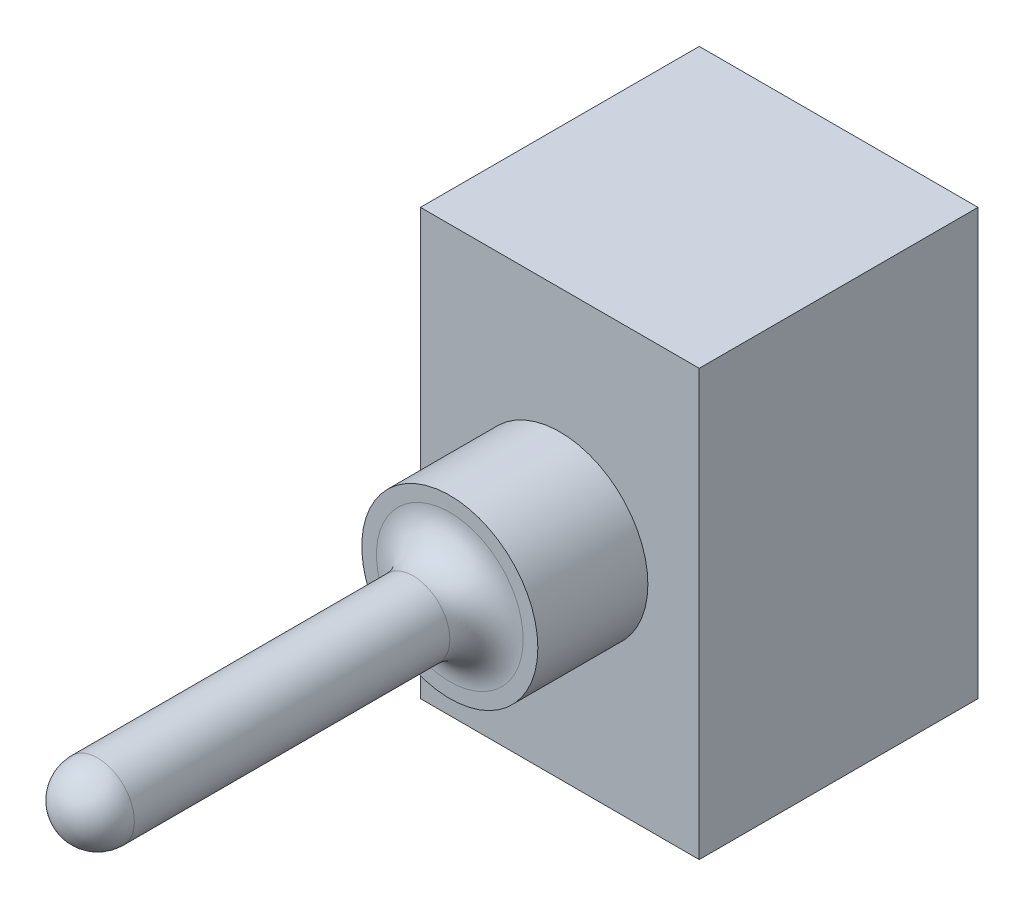
SolidWorks part; units mm, degrees
ref_plane "Plan de face" through (0, 0, 0) normal (0, 0, 1) x (1, 0, 0)
ref_plane "Plan de dessus" through (0, 0, 0) normal (0, 1, 0) x (1, 0, 0)
ref_plane "Plan de droite" through (0, 0, 0) normal (1, 0, 0) x (0, 0, -1)
sketch "Esquisse1" plane through (0, 0, 0) normal (0, 0, 1) x (1, 0, 0)
  line L1 (-63.8068, 29.1818) -> (-44.8068, 29.1818)
  line L2 (-63.8068, 29.1818) -> (-63.8068, 0.1818)
  line L3 (-63.8068, 0.1818) -> (-44.8068, 0.1818)
  line L4 (-44.8068, 29.1818) -> (-44.8068, 0.1818)
  dimension "D1" = 19
  dimension "D2" = 29
extrude "Boss.-Extru.1" add sketch "Esquisse1" along normal blind 19
sketch "Esquisse3" plane through (0, 0, 19) normal (0, 0, 1) x (1, 0, 0)
  line L0 (-44.8068, 0.1818) -> (-44.8068, 29.1818) construction
  line L1 (-63.8068, 0.1818) -> (-44.8068, 0.1818) construction
  circle A0 centre (-54.3068, 14.6818) radius 6
  point P2 (-44.8068, 14.6818)
  point P5 (-54.3068, 0.1818)
  dimension "D3" = 12
  dimension "D1" = 0
  dimension "D2" = 0
extrude "Boss.-Extru.2" add sketch "Esquisse3" along normal blind 7.5
sketch "Esquisse4" plane through (0, 0, 26.5) normal (0, 0, 1) x (1, 0, 0)
  circle A0 centre (-54.3068, 14.6818) radius 2.5
  circle A1 centre (-54.3068, 14.6818) radius 6 construction
  dimension "D2" = 5
  dimension "D1" = 0
extrude "Boss.-Extru.3" add sketch "Esquisse4" along normal blind 26.5
fillet "Congé3" radius 2.5 2 edges at (-51.8068, 14.6818, 26.5) (-51.8068, 14.6818, 53)
